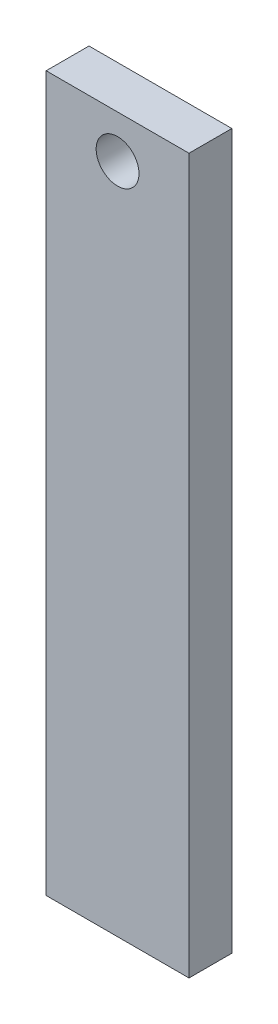
SolidWorks part; units mm, degrees
ref_plane "Front Plane" through (0, 0, 0) normal (0, 0, 1) x (1, 0, 0)
ref_plane "Top Plane" through (0, 0, 0) normal (0, 1, 0) x (1, 0, 0)
ref_plane "Right Plane" through (0, 0, 0) normal (1, 0, 0) x (0, 0, -1)
sketch "Sketch1" plane through (0, 0, 0) normal (0, 1, 0) x (1, 0, 0)
  line L1 (-25, 7.5) -> (25, 7.5)
  line L2 (-25, 7.5) -> (-25, -7.5)
  line L3 (-25, -7.5) -> (25, -7.5)
  line L4 (25, 7.5) -> (25, -7.5)
  line L5 (-25, 7.5) -> (25, -7.5) construction
  line L6 (-25, -7.5) -> (25, 7.5) construction
  point P0 (0, 0)
  dimension "D1" = 50
  dimension "D2" = 15
extrude "Boss-Extrude1" add sketch "Sketch1" along normal blind 250
sketch "Sketch2" plane through (0, 0, 7.5) normal (0, 0, 1) x (1, 0, 0)
  line L0 (-25, 250) -> (-25, 0) construction
  circle A0 centre (0, 235.0492) radius 7.5
  dimension "D1" = 15
  dimension "D2" = 25
extrude "Cut-Extrude2" cut sketch "Sketch2" against normal through all
